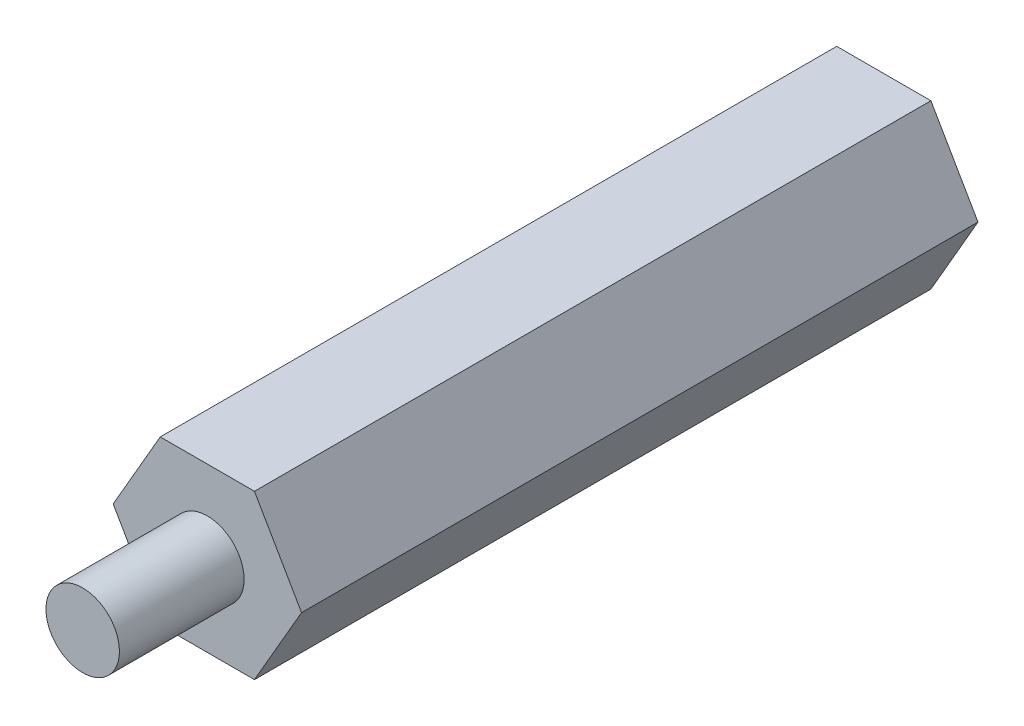
SolidWorks part; units mm, degrees
ref_plane "Plan de face" through (0, 0, 0) normal (0, 0, 1) x (1, 0, 0)
ref_plane "Plan de dessus" through (0, 0, 0) normal (0, 1, 0) x (1, 0, 0)
ref_plane "Plan de droite" through (0, 0, 0) normal (1, 0, 0) x (0, 0, -1)
sketch "Esquisse1" plane through (0, 0, 0) normal (0, 0, 1) x (1, 0, 0)
  line L1 (3.5507, 0) -> (1.7754, 3.075)
  line L2 (1.7754, 3.075) -> (-1.7754, 3.075)
  line L3 (-1.7754, 3.075) -> (-3.5507, 0)
  line L4 (-3.5507, 0) -> (-1.7754, -3.075)
  line L5 (-1.7754, -3.075) -> (1.7754, -3.075)
  line L6 (1.7754, -3.075) -> (3.5507, 0)
  circle A0 centre (0, 0) radius 3.075 construction
extrude "Boss.-Extru.1" add sketch "Esquisse1" along normal blind 25.5
sketch "Esquisse2" plane through (0, 0, 25.5) normal (0, 0, 1) x (1, 0, 0)
  circle A0 centre (0, 0) radius 1.385
extrude "Boss.-Extru.2" add sketch "Esquisse2" along normal blind 4.7
sketch "Esquisse3" plane through (0, 0, 0) normal (0, 0, -1) x (-1, 0, 0)
  circle A0 centre (0, 0) radius 1.35
extrude "Enlèv. mat.-Extru.1" cut sketch "Esquisse3" against normal blind 4.7
